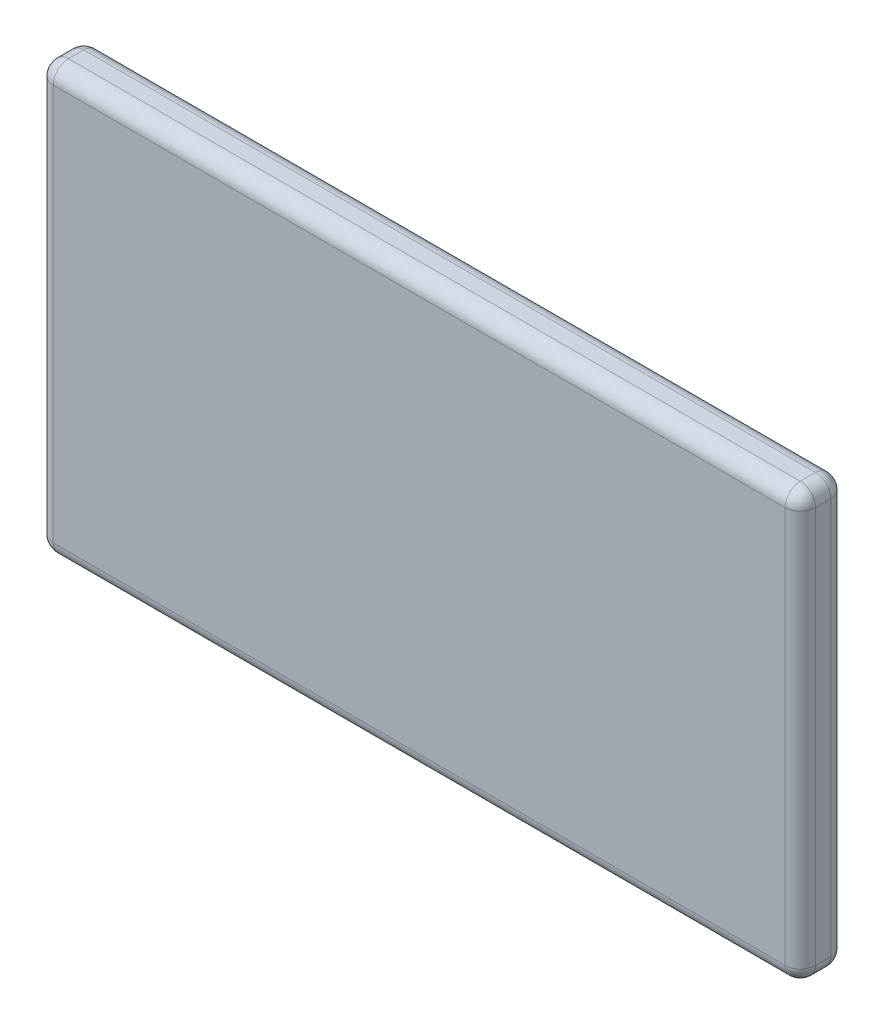
SolidWorks part; units mm, degrees
material "Nickel"
ref_plane "Front Plane" through (0, 0, 0) normal (0, 0, 1) x (1, 0, 0)
ref_plane "Top Plane" through (0, 0, 0) normal (0, 1, 0) x (1, 0, 0)
ref_plane "Right Plane" through (0, 0, 0) normal (1, 0, 0) x (0, 0, -1)
sketch "Sketch2" plane through (0, 0, 0) normal (0, 0, 1) x (1, 0, 0)
  line L1 (12.5, -7) -> (-12.5, -7)
  line L2 (12.5, -7) -> (12.5, 7)
  line L3 (12.5, 7) -> (-12.5, 7)
  line L4 (-12.5, -7) -> (-12.5, 7)
  line L5 (12.5, -7) -> (-12.5, 7) construction
  line L6 (12.5, 7) -> (-12.5, -7) construction
  point P0 (0, 0)
  dimension "D1" = 25
  dimension "D2" = 14
extrude "Boss-Extrude1" add sketch "Sketch2" along normal blind 1.5
fillet "Fillet1" radius 0.5 12 edges at (0, -7, 1.5) (0, 7, 1.5) (-12.5, 7, 0.75) (12.5, 7, 0.75) (12.5, -7, 0.75) (-12.5, -7, 0.75) (0, -7, 0) (-12.5, 0, 0) (-12.5, 0, 1.5) (12.5, 0, 1.5) (12.5, 0, 0) (0, 7, 0)
